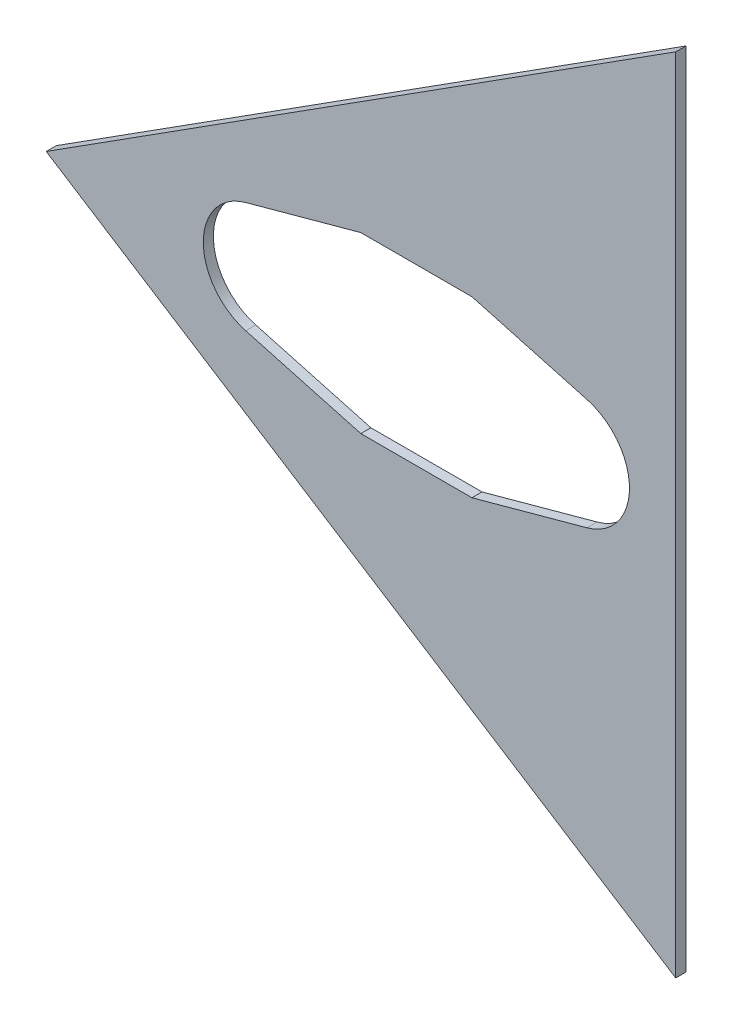
SolidWorks part; units mm, degrees
ref_plane "Front Plane" through (0, 0, 0) normal (0, 0, 1) x (1, 0, 0)
ref_plane "Top Plane" through (0, 0, 0) normal (0, 1, 0) x (1, 0, 0)
ref_plane "Right Plane" through (0, 0, 0) normal (1, 0, 0) x (0, 0, -1)
sketch "Sketch1" plane through (0, 0, 0) normal (0, 0, 1) x (1, 0, 0)
  line L0 (0, 0) -> (-209.5838, 0) construction
  line L1 (228.2329, 307.5059) -> (-209.5838, 0.9433)
  line L2 (-209.5838, -0.9433) -> (228.2329, -307.5059)
  line L3 (244.9564, -271.6422) -> (244.9564, 271.6422)
  line L5 (251.3064, 273.05) -> (251.3064, -273.05) construction
  line L8 (220.3479, 339.4408) -> (180.2831, 425.36) construction
  line L9 (228.2329, 307.5059) -> (244.9564, 271.6422)
  line L11 (220.3479, -339.4408) -> (248.9266, -278.1535) construction
  line L12 (244.9564, -271.6422) -> (228.2329, -307.5059)
  line L16 (-209.5838, -0.9433) -> (-209.5838, 0.9433)
  point P11 (0, 0)
  dimension "D1" = 6.35
  dimension "D2" = 70
  dimension "D3" = 615.0117
  dimension "D4" = 6.35
  dimension "D5" = 6.35
extrude "Boss-Extrude1" add sketch "Sketch1" along normal blind 6.35
sketch "Sketch2" plane through (0, 0, 0) normal (0, 0, -1) x (-1, 0, 0)
  line L67 (-46.1857, -54.9274) -> (26.5054, -35.0337)
  line L68 (-116.3212, -54.9274) -> (-46.1857, -54.9274)
  line L69 (-189.0123, -35.0337) -> (-116.3212, -54.9274)
  line L70 (-116.3212, 54.9274) -> (-189.0123, 35.0337)
  line L71 (-46.1857, 54.9274) -> (-116.3212, 54.9274)
  line L72 (26.5054, 35.0337) -> (-46.1857, 54.9274)
  line L73 (-46.1857, -54.9274) -> (26.5054, -35.0337)
  line L74 (-116.3212, -54.9274) -> (-46.1857, -54.9274)
  line L75 (-189.0123, -35.0337) -> (-116.3212, -54.9274)
  line L76 (-116.3212, 54.9274) -> (-189.0123, 35.0337)
  line L77 (-46.1857, 54.9274) -> (-116.3212, 54.9274)
  line L78 (26.5054, 35.0337) -> (-46.1857, 54.9274)
  arc A22 (-189.0123, 35.0337) -> (-189.0123, -35.0337) centre (-179.4244, 0) ccw
  arc A23 (26.5054, -35.0337) -> (26.5054, 35.0337) centre (16.9176, 0) ccw
  arc A24 (-189.0123, 35.0337) -> (-189.0123, -35.0337) centre (-179.4244, 0) ccw
  arc A25 (26.5054, -35.0337) -> (26.5054, 35.0337) centre (16.9176, 0) ccw
  dimension "D1" = 6.35
extrude "Cut-Extrude1" cut sketch "Sketch2" against normal through all
sketch "Sketch3" plane through (0, 0, 0) normal (0, 0, 1) x (1, 0, 0)
  line L0 (244.9564, -253.144) -> (-152.4, 0)
  line L1 (244.9564, -271.6422) -> (244.9564, 271.6422) construction
  line L2 (-152.4, 0) -> (6.3571, 0) construction
  line L3 (244.9564, -253.144) -> (244.9564, 253.144)
  line L4 (244.9564, 253.144) -> (-152.4, 0)
  point P7 (244.9564, 0)
  dimension "D1" = 152.4
  dimension "D2" = 65
extrude "Cut-Extrude6" cut sketch "Sketch3" along normal through all flip side to cut
